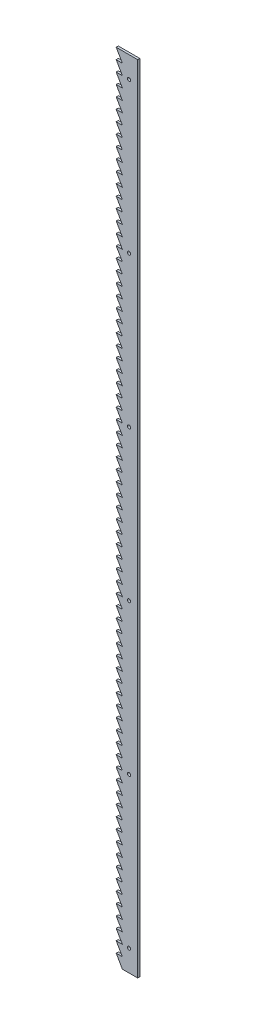
SolidWorks part; units mm, degrees
material "St.37"
ref_plane "Front Plane" through (0, 0, 0) normal (0, 0, 1) x (1, 0, 0)
ref_plane "Top Plane" through (0, 0, 0) normal (0, 1, 0) x (1, 0, 0)
ref_plane "Right Plane" through (0, 0, 0) normal (1, 0, 0) x (0, 0, -1)
sketch "Sketch1" plane through (0, 0, 0) normal (0, 0, 1) x (1, 0, 0)
  line L0 (0, 370) -> (0, -370)
  line L1 (0, 370) -> (-20, 370)
  line L2 (-20, 370) -> (-14.2265, 360)
  line L3 (-14.2265, 360) -> (-20, 360)
  line L4 (-20, 360) -> (-14.2265, 350)
  line L5 (-14.2265, 350) -> (-20, 350)
  line L6 (-20, 350) -> (-14.2265, 340)
  line L7 (-14.2265, 340) -> (-20, 340)
  line L8 (-20, 340) -> (-14.2265, 330)
  line L9 (-14.2265, 330) -> (-20, 330)
  line L10 (-20, 330) -> (-14.2265, 320)
  line L11 (-14.2265, 320) -> (-20, 320)
  line L12 (-20, 320) -> (-14.2265, 310)
  line L13 (-14.2265, 310) -> (-20, 310)
  line L14 (-20, 310) -> (-14.2265, 300)
  line L15 (-14.2265, 300) -> (-20, 300)
  line L16 (-20, 300) -> (-14.2265, 290)
  line L17 (-14.2265, 290) -> (-20, 290)
  line L18 (-20, 290) -> (-14.2265, 280)
  line L19 (-14.2265, 280) -> (-20, 280)
  line L20 (-20, 280) -> (-14.2265, 270)
  line L21 (-14.2265, 270) -> (-20, 270)
  line L22 (-20, 270) -> (-14.2265, 260)
  line L23 (-14.2265, 260) -> (-20, 260)
  line L24 (-20, 260) -> (-14.2265, 250)
  line L25 (-14.2265, 250) -> (-20, 250)
  line L26 (-20, 250) -> (-14.2265, 240)
  line L27 (-14.2265, 240) -> (-20, 240)
  line L28 (-20, 240) -> (-14.2265, 230)
  line L29 (-14.2265, 230) -> (-20, 230)
  line L30 (-20, 230) -> (-14.2265, 220)
  line L31 (-14.2265, 220) -> (-20, 220)
  line L32 (-20, 220) -> (-14.2265, 210)
  line L33 (-14.2265, 210) -> (-20, 210)
  line L34 (-20, 210) -> (-14.2265, 200)
  line L35 (-14.2265, 200) -> (-20, 200)
  line L36 (-20, 200) -> (-14.2265, 190)
  line L37 (-14.2265, 190) -> (-20, 190)
  line L38 (-20, 190) -> (-14.2265, 180)
  line L39 (-14.2265, 180) -> (-20, 180)
  line L40 (-20, 180) -> (-14.2265, 170)
  line L41 (-14.2265, 170) -> (-20, 170)
  line L42 (-20, 170) -> (-14.2265, 160)
  line L43 (-14.2265, 160) -> (-20, 160)
  line L44 (-20, 160) -> (-14.2265, 150)
  line L45 (-14.2265, 150) -> (-20, 150)
  line L46 (-20, 150) -> (-14.2265, 140)
  line L47 (-14.2265, 140) -> (-20, 140)
  line L48 (-20, 140) -> (-14.2265, 130)
  line L49 (-14.2265, 130) -> (-20, 130)
  line L50 (-20, 130) -> (-14.2265, 120)
  line L51 (-14.2265, 120) -> (-20, 120)
  line L52 (-20, 120) -> (-14.2265, 110)
  line L53 (-14.2265, 110) -> (-20, 110)
  line L54 (-20, 110) -> (-14.2265, 100)
  line L55 (-14.2265, 100) -> (-20, 100)
  line L56 (-20, 100) -> (-14.2265, 90)
  line L57 (-14.2265, 90) -> (-20, 90)
  line L58 (-20, 90) -> (-14.2265, 80)
  line L59 (-14.2265, 80) -> (-20, 80)
  line L60 (-20, 80) -> (-14.2265, 70)
  line L61 (-14.2265, 70) -> (-20, 70)
  line L62 (-20, 70) -> (-14.2265, 60)
  line L63 (-14.2265, 60) -> (-20, 60)
  line L64 (-20, 60) -> (-14.2265, 50)
  line L65 (-14.2265, 50) -> (-20, 50)
  line L66 (-20, 50) -> (-14.2265, 40)
  line L67 (-14.2265, 40) -> (-20, 40)
  line L68 (-20, 40) -> (-14.2265, 30)
  line L69 (-14.2265, 30) -> (-20, 30)
  line L70 (-20, 30) -> (-14.2265, 20)
  line L71 (-14.2265, 20) -> (-20, 20)
  line L72 (-20, 20) -> (-14.2265, 10)
  line L73 (-14.2265, 10) -> (-20, 10)
  line L74 (-20, 10) -> (-14.2265, 0)
  line L75 (-14.2265, 0) -> (-20, 0)
  line L76 (-20, 0) -> (-14.2265, -10)
  line L77 (-14.2265, -10) -> (-20, -10)
  line L78 (-20, -10) -> (-14.2265, -20)
  line L79 (-14.2265, -20) -> (-20, -20)
  line L80 (-20, -20) -> (-14.2265, -30)
  line L81 (-14.2265, -30) -> (-20, -30)
  line L82 (-20, -30) -> (-14.2265, -40)
  line L83 (-14.2265, -40) -> (-20, -40)
  line L84 (-20, -40) -> (-14.2265, -50)
  line L85 (-14.2265, -50) -> (-20, -50)
  line L86 (-20, -50) -> (-14.2265, -60)
  line L87 (-14.2265, -60) -> (-20, -60)
  line L88 (-20, -60) -> (-14.2265, -70)
  line L89 (-14.2265, -70) -> (-20, -70)
  line L90 (-20, -70) -> (-14.2265, -80)
  line L91 (-14.2265, -80) -> (-20, -80)
  line L92 (-20, -80) -> (-14.2265, -90)
  line L93 (-14.2265, -90) -> (-20, -90)
  line L94 (-20, -90) -> (-14.2265, -100)
  line L95 (-14.2265, -100) -> (-20, -100)
  line L96 (-20, -100) -> (-14.2265, -110)
  line L97 (-14.2265, -110) -> (-20, -110)
  line L98 (-20, -110) -> (-14.2265, -120)
  line L99 (-14.2265, -120) -> (-20, -120)
  line L100 (-20, -120) -> (-14.2265, -130)
  line L101 (-14.2265, -130) -> (-20, -130)
  line L102 (-20, -130) -> (-14.2265, -140)
  line L103 (-14.2265, -140) -> (-20, -140)
  line L104 (-20, -140) -> (-14.2265, -150)
  line L105 (-14.2265, -150) -> (-20, -150)
  line L106 (-20, -150) -> (-14.2265, -160)
  line L107 (-14.2265, -160) -> (-20, -160)
  line L108 (-20, -160) -> (-14.2265, -170)
  line L109 (-14.2265, -170) -> (-20, -170)
  line L110 (-20, -170) -> (-14.2265, -180)
  line L111 (-14.2265, -180) -> (-20, -180)
  line L112 (-20, -180) -> (-14.2265, -190)
  line L113 (-14.2265, -190) -> (-20, -190)
  line L114 (-20, -190) -> (-14.2265, -200)
  line L115 (-14.2265, -200) -> (-20, -200)
  line L116 (-20, -200) -> (-14.2265, -210)
  line L117 (-14.2265, -210) -> (-20, -210)
  line L118 (-20, -210) -> (-14.2265, -220)
  line L119 (-14.2265, -220) -> (-20, -220)
  line L120 (-20, -220) -> (-14.2265, -230)
  line L121 (-14.2265, -230) -> (-20, -230)
  line L122 (-20, -230) -> (-14.2265, -240)
  line L123 (-14.2265, -240) -> (-20, -240)
  line L124 (-20, -240) -> (-14.2265, -250)
  line L125 (-14.2265, -250) -> (-20, -250)
  line L126 (-20, -250) -> (-14.2265, -260)
  line L127 (-14.2265, -260) -> (-20, -260)
  line L128 (-20, -260) -> (-14.2265, -270)
  line L129 (-14.2265, -270) -> (-20, -270)
  line L130 (-20, -270) -> (-14.2265, -280)
  line L131 (-14.2265, -280) -> (-20, -280)
  line L132 (-20, -280) -> (-14.2265, -290)
  line L133 (-14.2265, -290) -> (-20, -290)
  line L134 (-20, -290) -> (-14.2265, -300)
  line L135 (-14.2265, -300) -> (-20, -300)
  line L136 (-20, -300) -> (-14.2265, -310)
  line L137 (-14.2265, -310) -> (-20, -310)
  line L138 (-20, -310) -> (-14.2265, -320)
  line L139 (-14.2265, -320) -> (-20, -320)
  line L140 (-20, -320) -> (-14.2265, -330)
  line L141 (-14.2265, -330) -> (-20, -330)
  line L142 (-20, -330) -> (-14.2265, -340)
  line L143 (-14.2265, -340) -> (-20, -340)
  line L144 (-20, -340) -> (-14.2265, -350)
  line L145 (-14.2265, -350) -> (-20, -350)
  line L146 (-20, -350) -> (-14.2265, -360)
  line L147 (-14.2265, -360) -> (-20, -360)
  line L148 (-20, -360) -> (-14.2265, -370)
  line L150 (-14.2265, -370) -> (0, -370)
  line L152 (-14.2265, -370) -> (-20, -370) [skipped]
  circle A0 centre (-8, 350) radius 1.5
  circle A1 centre (-8, 210) radius 1.5
  circle A2 centre (-8, 70) radius 1.5
  circle A3 centre (-8, -70) radius 1.5
  circle A4 centre (-8, -210) radius 1.5
  circle A5 centre (-8, -350) radius 1.5
  point P3 (0, 0)
  dimension "D5" = 8
  dimension "D9" = 20
  dimension "D10" = 3
  dimension "D1" = 740
  dimension "D2" = 60
  dimension "D3" = 10
  dimension "D4" = 20
  dimension "D8" = 20
  dimension "D6" = 74
  dimension "D7" = 6
extrude "Boss-Extrude1" add sketch "Sketch1" along normal blind 2 contours L148 L150 L0 L1 L2 L3 L4 L5 L6 L7 L8 L9 L10 L11 L12 L13 L14 L15 L16 L17 L18 L19 L20 L21 L22 L23 L24 L25 L26 L27 L28 L29 L30 L31 L32 L33 L34 L35 L36 L37 L38 L39 L40 L41 L42 L43 L44 L45 L46 L47 L48
